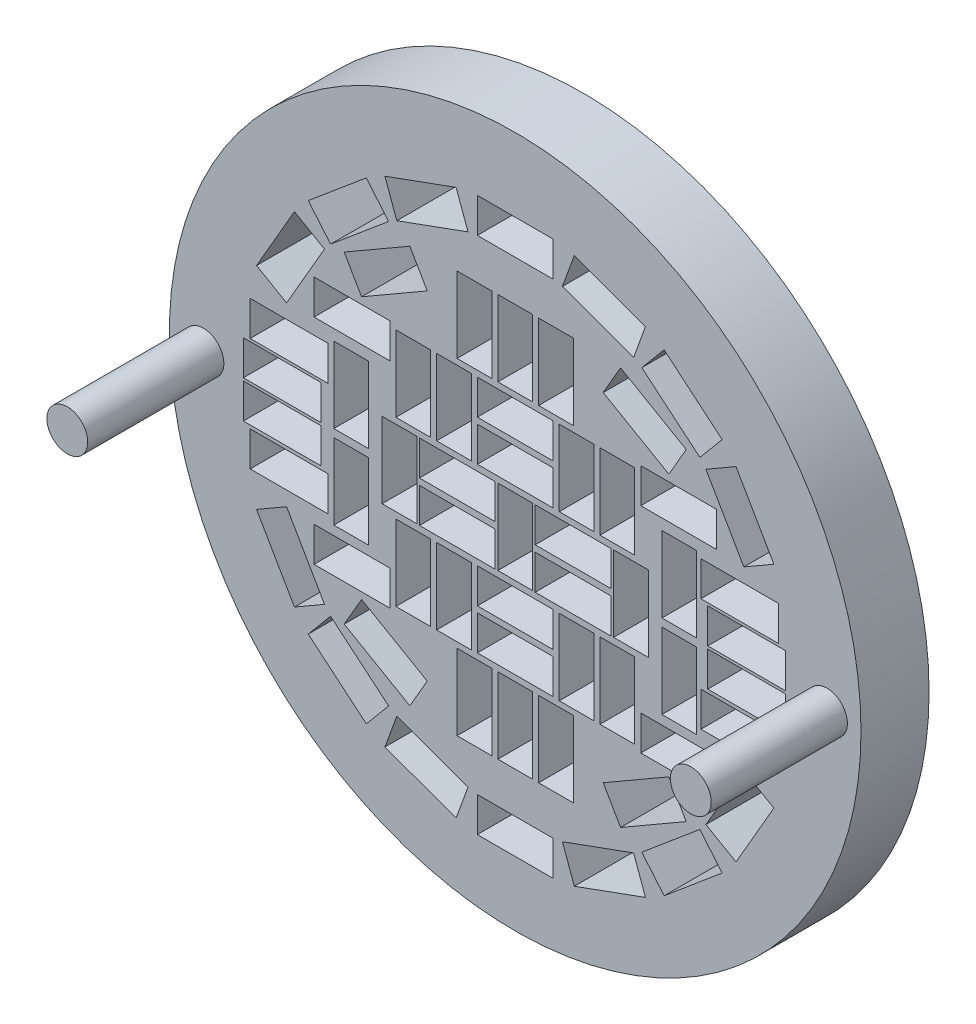
SolidWorks part; units mm, degrees
material "PBT à usage général"
ref_plane "Plan de face" through (0, 0, 0) normal (0, 0, 1) x (1, 0, 0)
ref_plane "Plan de dessus" through (0, 0, 0) normal (0, 1, 0) x (1, 0, 0)
ref_plane "Plan de droite" through (0, 0, 0) normal (1, 0, 0) x (0, 0, -1)
sketch "Esquisse1" plane through (0, 0, 0) normal (0, 0, 1) x (1, 0, 0)
  circle A0 centre (16.6252, 7.1087) radius 25.4
  dimension "D1" = 50.8
extrude "Boss.-Extru.1" add sketch "Esquisse1" along normal blind 5
sketch "Esquisse2" plane through (0, 0, 5) normal (0, 0, 1) x (1, 0, 0)
  line L0 (15.1552, 7.0089) -> (15.1552, 9.5589)
  line L1 (23.8502, 4.0022) -> (23.8502, 9.5672)
  line L2 (15.3502, 4.0022) -> (17.9002, 4.0022)
  line L3 (15.3502, 4.0022) -> (15.3502, 9.5672)
  line L4 (15.3502, 9.5672) -> (17.9002, 9.5672)
  line L5 (17.9002, 4.0022) -> (17.9002, 9.5672)
  line L6 (15.3502, 4.0022) -> (17.9002, 9.5672) construction
  line L7 (15.3502, 9.5672) -> (17.9002, 4.0022) construction
  line L8 (23.8502, 4.0022) -> (26.4002, 4.0022)
  line L9 (26.4002, 4.0022) -> (26.4002, 9.5672)
  line L10 (23.8502, 9.5672) -> (26.4002, 9.5672)
  line L11 (23.8502, 16.0022) -> (23.8502, 21.5672) [skipped]
  line L12 (23.8502, 16.0022) -> (26.4002, 16.0022) [skipped]
  line L13 (26.4002, 16.0022) -> (26.4002, 21.5672) [skipped]
  line L14 (23.8502, 21.5672) -> (26.4002, 21.5672) [skipped]
  line L15 (15.3502, 16.0022) -> (15.3502, 21.5672)
  line L16 (15.3502, 16.0022) -> (17.9002, 16.0022)
  line L17 (17.9002, 16.0022) -> (17.9002, 21.5672)
  line L18 (15.3502, 21.5672) -> (17.9002, 21.5672)
  line L19 (6.8502, 4.0022) -> (6.8502, 9.5672)
  line L20 (6.8502, 4.0022) -> (9.4002, 4.0022)
  line L21 (9.4002, 4.0022) -> (9.4002, 9.5672)
  line L22 (6.8502, 9.5672) -> (9.4002, 9.5672)
  line L23 (6.8502, -7.9978) -> (6.8502, -2.4328) [skipped]
  line L24 (6.8502, -7.9978) -> (9.4002, -7.9978) [skipped]
  line L25 (9.4002, -7.9978) -> (9.4002, -2.4328) [skipped]
  line L26 (6.8502, -2.4328) -> (9.4002, -2.4328) [skipped]
  line L27 (15.3502, -7.9978) -> (15.3502, -2.4328)
  line L28 (15.3502, -7.9978) -> (17.9002, -7.9978)
  line L29 (17.9002, -7.9978) -> (17.9002, -2.4328)
  line L30 (15.3502, -2.4328) -> (17.9002, -2.4328)
  line L31 (23.6552, 7.0089) -> (18.0902, 7.0089)
  line L32 (15.3502, 21.5672) -> (17.9002, 16.0022) construction
  line L33 (23.6552, 7.0089) -> (23.6552, 9.5589)
  line L34 (23.6552, 9.5589) -> (18.0902, 9.5589)
  line L35 (18.0902, 7.0089) -> (18.0902, 9.5589)
  line L36 (23.6552, 7.0089) -> (18.0902, 9.5589) construction
  line L37 (23.6552, 9.5589) -> (18.0902, 7.0089) construction
  line L38 (15.1552, 7.0089) -> (9.5902, 7.0089)
  line L39 (9.5902, 7.0089) -> (9.5902, 9.5589)
  line L40 (15.1552, 9.5589) -> (9.5902, 9.5589)
  line L41 (15.1552, 3.9889) -> (15.1552, 6.5389)
  line L42 (15.1552, 3.9889) -> (9.5902, 3.9889)
  line L43 (9.5902, 3.9889) -> (9.5902, 6.5389)
  line L44 (15.1552, 6.5389) -> (9.5902, 6.5389)
  line L45 (23.6552, 3.9889) -> (23.6552, 6.5389)
  line L46 (23.6552, 3.9889) -> (18.0902, 3.9889)
  line L47 (18.0902, 3.9889) -> (18.0902, 6.5389)
  line L48 (23.6552, 6.5389) -> (18.0902, 6.5389)
  line L49 (16.6252, 6.7847) -> (16.6252, 18.7847) construction
  line L50 (19.4077, 1.0032) -> (19.4077, 3.5532)
  line L51 (19.4077, 10.0102) -> (13.8427, 10.0102)
  line L52 (19.4077, 10.0102) -> (19.4077, 12.5602)
  line L53 (19.4077, 12.5602) -> (13.8427, 12.5602)
  line L54 (13.8427, 10.0102) -> (13.8427, 12.5602)
  line L55 (19.4077, 10.0102) -> (13.8427, 12.5602) construction
  line L56 (19.4077, 12.5602) -> (13.8427, 10.0102) construction
  line L57 (19.4077, 13.0032) -> (13.8427, 13.0032)
  line L58 (19.4077, 13.0032) -> (19.4077, 15.5532)
  line L59 (19.4077, 15.5532) -> (13.8427, 15.5532)
  line L60 (13.8427, 13.0032) -> (13.8427, 15.5532)
  line L61 (19.4077, 13.0032) -> (13.8427, 15.5532) construction
  line L62 (19.4077, 15.5532) -> (13.8427, 13.0032) construction
  line L63 (19.4077, 1.0032) -> (13.8427, 1.0032)
  line L64 (13.8427, 1.0032) -> (13.8427, 3.5532)
  line L65 (19.4077, 3.5532) -> (13.8427, 3.5532)
  line L66 (19.4077, -1.9898) -> (19.4077, 0.5602)
  line L67 (19.4077, -1.9898) -> (13.8427, -1.9898)
  line L68 (13.8427, -1.9898) -> (13.8427, 0.5602)
  line L69 (19.4077, 0.5602) -> (13.8427, 0.5602)
  line L70 (16.6252, 12.7847) -> (12.1247, 12.7847) construction
  line L71 (10.8497, 10.0022) -> (13.3997, 10.0022)
  line L72 (10.8497, 10.0022) -> (10.8497, 15.5672)
  line L73 (10.8497, 15.5672) -> (13.3997, 15.5672)
  line L74 (13.3997, 10.0022) -> (13.3997, 15.5672)
  line L75 (10.8497, 10.0022) -> (13.3997, 15.5672) construction
  line L76 (10.8497, 15.5672) -> (13.3997, 10.0022) construction
  line L77 (7.8597, 10.0022) -> (7.8597, 15.5672)
  line L78 (7.8597, 10.0022) -> (10.4097, 10.0022)
  line L79 (10.4097, 10.0022) -> (10.4097, 15.5672)
  line L80 (7.8597, 15.5672) -> (10.4097, 15.5672)
  line L81 (19.8597, 10.0022) -> (19.8597, 15.5672)
  line L82 (19.8597, 15.5672) -> (22.4097, 15.5672)
  line L83 (22.4097, 10.0022) -> (22.4097, 15.5672)
  line L84 (19.8597, 10.0022) -> (22.4097, 10.0022)
  line L85 (22.8497, 10.0022) -> (22.8497, 15.5672)
  line L86 (22.8497, 10.0022) -> (25.3997, 10.0022)
  line L87 (25.3997, 10.0022) -> (25.3997, 15.5672)
  line L88 (22.8497, 15.5672) -> (25.3997, 15.5672)
  line L89 (19.8597, -2.0278) -> (19.8597, 3.5372)
  line L90 (19.8597, 3.5372) -> (22.4097, 3.5372)
  line L91 (22.4097, -2.0278) -> (22.4097, 3.5372)
  line L92 (19.8597, -2.0278) -> (22.4097, -2.0278)
  line L93 (22.8497, -2.0278) -> (22.8497, 3.5372)
  line L94 (22.8497, -2.0278) -> (25.3997, -2.0278)
  line L95 (25.3997, -2.0278) -> (25.3997, 3.5372)
  line L96 (22.8497, 3.5372) -> (25.3997, 3.5372)
  line L97 (7.8597, -2.0278) -> (7.8597, 3.5372)
  line L98 (7.8597, 3.5372) -> (10.4097, 3.5372)
  line L99 (10.4097, -2.0278) -> (10.4097, 3.5372)
  line L100 (7.8597, -2.0278) -> (10.4097, -2.0278)
  line L101 (10.8497, -2.0278) -> (10.8497, 3.5372)
  line L102 (10.8497, -2.0278) -> (13.3997, -2.0278)
  line L103 (13.3997, -2.0278) -> (13.3997, 3.5372)
  line L104 (10.8497, 3.5372) -> (13.3997, 3.5372)
  line L105 (25.3219, 22.5432) -> (26.194, 24.9394)
  line L106 (19.4077, 24.5672) -> (13.8427, 24.5672)
  line L107 (19.4077, 24.5672) -> (19.4077, 27.1172)
  line L108 (19.4077, 27.1172) -> (13.8427, 27.1172)
  line L109 (13.8427, 24.5672) -> (13.8427, 27.1172)
  line L110 (19.4077, 24.5672) -> (13.8427, 27.1172) construction
  line L111 (19.4077, 27.1172) -> (13.8427, 24.5672) construction
  line L112 (25.3219, 22.5432) -> (20.0925, 24.4465)
  line L113 (20.0925, 24.4465) -> (20.9646, 26.8427)
  line L114 (26.194, 24.9394) -> (20.9646, 26.8427)
  line L115 (30.1871, 18.6184) -> (31.8262, 20.5718)
  line L116 (30.1871, 18.6184) -> (25.9241, 22.1955)
  line L117 (25.9241, 22.1955) -> (27.5632, 24.1489)
  line L118 (31.8262, 20.5718) -> (27.5632, 24.1489)
  line L119 (33.4166, 13.2663) -> (35.6249, 14.5413)
  line L120 (33.4166, 13.2663) -> (30.6341, 18.0857)
  line L121 (30.6341, 18.0857) -> (32.8424, 19.3607)
  line L122 (35.6249, 14.5413) -> (32.8424, 19.3607)
  line L123 (34.6207, 7.1324) -> (37.132, 7.5752) [skipped]
  line L124 (34.6207, 7.1324) -> (33.6544, 12.6129) [skipped]
  line L125 (33.6544, 12.6129) -> (36.1656, 13.0557) [skipped]
  line L126 (37.132, 7.5752) -> (36.1656, 13.0557) [skipped]
  line L127 (33.6544, 0.9566) -> (36.1656, 0.5138) [skipped]
  line L128 (33.6544, 0.9566) -> (34.6207, 6.4371) [skipped]
  line L129 (34.6207, 6.4371) -> (37.132, 5.9943) [skipped]
  line L130 (36.1656, 0.5138) -> (37.132, 5.9943) [skipped]
  line L131 (30.6341, -4.5162) -> (32.8424, -5.7912)
  line L132 (30.6341, -4.5162) -> (33.4166, 0.3032)
  line L133 (33.4166, 0.3032) -> (35.6249, -0.9718)
  line L134 (32.8424, -5.7912) -> (35.6249, -0.9718)
  line L135 (25.9241, -8.626) -> (27.5632, -10.5794)
  line L136 (25.9241, -8.626) -> (30.1871, -5.0489)
  line L137 (30.1871, -5.0489) -> (31.8262, -7.0023)
  line L138 (27.5632, -10.5794) -> (31.8262, -7.0023)
  line L139 (20.0925, -10.877) -> (20.9646, -13.2732)
  line L140 (20.0925, -10.877) -> (25.3219, -8.9737)
  line L141 (25.3219, -8.9737) -> (26.194, -11.3699)
  line L142 (20.9646, -13.2732) -> (26.194, -11.3699)
  line L143 (13.8427, -10.9978) -> (13.8427, -13.5478)
  line L144 (13.8427, -10.9978) -> (19.4077, -10.9978)
  line L145 (19.4077, -10.9978) -> (19.4077, -13.5478)
  line L146 (13.8427, -13.5478) -> (19.4077, -13.5478)
  line L147 (7.9285, -8.9737) -> (7.0564, -11.3699)
  line L148 (7.9285, -8.9737) -> (13.1579, -10.877)
  line L149 (13.1579, -10.877) -> (12.2858, -13.2732)
  line L150 (7.0564, -11.3699) -> (12.2858, -13.2732)
  line L151 (3.0633, -5.0489) -> (1.4242, -7.0023)
  line L152 (3.0633, -5.0489) -> (7.3264, -8.626)
  line L153 (7.3264, -8.626) -> (5.6872, -10.5794)
  line L154 (1.4242, -7.0023) -> (5.6872, -10.5794)
  line L155 (-0.1661, 0.3032) -> (-2.3745, -0.9718)
  line L156 (-0.1661, 0.3032) -> (2.6164, -4.5162)
  line L157 (2.6164, -4.5162) -> (0.408, -5.7912)
  line L158 (-2.3745, -0.9718) -> (0.408, -5.7912)
  line L159 (-1.3703, 6.4371) -> (-3.8816, 5.9943) [skipped]
  line L160 (-1.3703, 6.4371) -> (-0.404, 0.9566) [skipped]
  line L161 (-0.404, 0.9566) -> (-2.9152, 0.5138) [skipped]
  line L162 (-3.8816, 5.9943) -> (-2.9152, 0.5138) [skipped]
  line L163 (-0.404, 12.6129) -> (-2.9152, 13.0557) [skipped]
  line L164 (-0.404, 12.6129) -> (-1.3703, 7.1324) [skipped]
  line L165 (-1.3703, 7.1324) -> (-3.8816, 7.5752) [skipped]
  line L166 (-2.9152, 13.0557) -> (-3.8816, 7.5752) [skipped]
  line L167 (2.6164, 18.0857) -> (0.408, 19.3607)
  line L168 (2.6164, 18.0857) -> (-0.1661, 13.2663)
  line L169 (-0.1661, 13.2663) -> (-2.3745, 14.5413)
  line L170 (0.408, 19.3607) -> (-2.3745, 14.5413)
  line L171 (7.3264, 22.1955) -> (5.6872, 24.1489)
  line L172 (7.3264, 22.1955) -> (3.0633, 18.6184)
  line L173 (3.0633, 18.6184) -> (1.4242, 20.5718)
  line L174 (5.6872, 24.1489) -> (1.4242, 20.5718)
  line L179 (14.9032, 21.5612) -> (14.9032, 15.9962)
  line L180 (20.8932, 21.5612) -> (18.3432, 21.5612)
  line L181 (20.8932, 21.5612) -> (20.8932, 15.9962)
  line L182 (20.8932, 15.9962) -> (18.3432, 15.9962)
  line L183 (18.3432, 21.5612) -> (18.3432, 15.9962)
  line L184 (20.8932, 21.5612) -> (18.3432, 15.9962) construction
  line L185 (20.8932, 15.9962) -> (18.3432, 21.5612) construction
  line L186 (14.9032, 21.5612) -> (12.3532, 21.5612)
  line L187 (12.3532, 21.5612) -> (12.3532, 15.9962)
  line L188 (14.9032, 15.9962) -> (12.3532, 15.9962)
  line L189 (14.9032, -2.4388) -> (14.9032, -8.0038)
  line L190 (14.9032, -2.4388) -> (12.3532, -2.4388)
  line L191 (12.3532, -2.4388) -> (12.3532, -8.0038)
  line L192 (14.9032, -8.0038) -> (12.3532, -8.0038)
  line L193 (20.8932, -2.4388) -> (20.8932, -8.0038)
  line L194 (20.8932, -2.4388) -> (18.3432, -2.4388)
  line L195 (18.3432, -2.4388) -> (18.3432, -8.0038)
  line L196 (20.8932, -8.0038) -> (18.3432, -8.0038)
  line L197 (5.8502, 7.0089) -> (5.8502, 12.5739)
  line L198 (29.9502, 7.0089) -> (27.4002, 7.0089)
  line L199 (29.9502, 7.0089) -> (29.9502, 12.5739)
  line L200 (29.9502, 12.5739) -> (27.4002, 12.5739)
  line L201 (27.4002, 7.0089) -> (27.4002, 12.5739)
  line L202 (29.9502, 7.0089) -> (27.4002, 12.5739) construction
  line L203 (29.9502, 12.5739) -> (27.4002, 7.0089) construction
  line L204 (5.8502, 7.0089) -> (3.3002, 7.0089)
  line L205 (3.3002, 7.0089) -> (3.3002, 12.5739)
  line L206 (5.8502, 12.5739) -> (3.3002, 12.5739)
  line L207 (5.8502, 0.8689) -> (5.8502, 6.4339)
  line L208 (5.8502, 0.8689) -> (3.3002, 0.8689)
  line L209 (3.3002, 0.8689) -> (3.3002, 6.4339)
  line L210 (5.8502, 6.4339) -> (3.3002, 6.4339)
  line L211 (29.9502, 0.8689) -> (29.9502, 6.4339)
  line L212 (29.9502, 0.8689) -> (27.4002, 0.8689)
  line L213 (27.4002, 0.8689) -> (27.4002, 6.4339)
  line L214 (29.9502, 6.4339) -> (27.4002, 6.4339)
  line L219 (13.1579, 24.4465) -> (12.2858, 26.8427)
  line L220 (13.1579, 24.4465) -> (7.9285, 22.5432)
  line L221 (7.9285, 22.5432) -> (7.0564, 24.9394)
  line L222 (12.2858, 26.8427) -> (7.0564, 24.9394)
  point P0 (16.6252, 18.7847)
  point P1 (16.6252, 18.7847)
  point P2 (20.8727, 8.2839)
  point P5 (16.6252, 6.7847)
  point P50 (16.6252, 11.2852)
  point P55 (16.6252, 14.2782)
  point P60 (12.1247, 12.7847)
  point P75 (16.6252, 25.8422)
  point P76 (9.1347, 12.7847)
  point P109 (19.6182, 18.7787)
  point P180 (16.6252, 6.7847)
  point P183 (28.6752, 9.7914)
  dimension "D1" = 5.565
  dimension "D2" = 2.55
  dimension "D7" = 12
  dimension "D8" = 0.19
  dimension "D11" = 0.443
  dimension "D12" = 0.443
  dimension "D14" = 2
  dimension "D15" = 0.443
  dimension "D18" = 3
  dimension "D20" = 0.443
  dimension "D21" = 0.443
  dimension "D24" = 1
  dimension "D3" = 2
  dimension "D4" = 2
  dimension "D5" = 2
  dimension "D6" = 2
  dimension "D9" = 2
  dimension "D10" = 2
  dimension "D13" = 2
  dimension "D16" = 2
  dimension "D17" = 2
  dimension "D22" = 2
  dimension "D23" = 2
  dimension "D25" = 2
  dimension "D26" = 2
  dimension "D19" = 18
extrude "Enlèv. mat.-Extru.1" cut sketch "Esquisse2" against normal through all
sketch "Esquisse3" plane through (0, 0, 5) normal (0, 0, 1) x (1, 0, 0)
  line L0 (3.3002, 12.5739) -> (3.3002, 7.0089) construction
  line L1 (2.8572, 9.6672) -> (-2.8428, 9.6672)
  line L2 (2.8572, 9.6672) -> (2.8572, 12.2172)
  line L3 (2.8572, 12.2172) -> (-2.8428, 12.2172)
  line L4 (-2.8428, 9.6672) -> (-2.8428, 12.2172)
  line L5 (2.8572, 9.6672) -> (-2.8428, 12.2172) construction
  line L6 (2.8572, 12.2172) -> (-2.8428, 9.6672) construction
  line L7 (9.4002, 9.5672) -> (6.8502, 9.5672) construction
  line L8 (35.9672, 9.6672) -> (35.9672, 12.2172)
  line L9 (35.9672, 9.6672) -> (30.2672, 9.6672)
  line L10 (30.2672, 9.6672) -> (30.2672, 12.2172)
  line L11 (35.9672, 12.2172) -> (30.2672, 12.2172)
  line L12 (35.9672, 1.3672) -> (35.9672, 3.9172)
  line L13 (35.9672, 1.3672) -> (30.2672, 1.3672)
  line L14 (30.2672, 1.3672) -> (30.2672, 3.9172)
  line L15 (35.9672, 3.9172) -> (30.2672, 3.9172)
  line L16 (2.8572, 1.3672) -> (2.8572, 3.9172)
  line L17 (2.8572, 1.3672) -> (-2.8428, 1.3672)
  line L18 (-2.8428, 1.3672) -> (-2.8428, 3.9172)
  line L19 (2.8572, 3.9172) -> (-2.8428, 3.9172)
  line L20 (36.4672, 6.9172) -> (36.4672, 9.4672)
  line L21 (2.3572, 6.9172) -> (-3.3428, 6.9172)
  line L22 (2.3572, 6.9172) -> (2.3572, 9.4672)
  line L23 (2.3572, 9.4672) -> (-3.3428, 9.4672)
  line L24 (-3.3428, 6.9172) -> (-3.3428, 9.4672)
  line L25 (2.3572, 6.9172) -> (-3.3428, 9.4672) construction
  line L26 (2.3572, 9.4672) -> (-3.3428, 6.9172) construction
  line L27 (36.4672, 6.9172) -> (30.7672, 6.9172)
  line L28 (30.7672, 6.9172) -> (30.7672, 9.4672)
  line L29 (36.4672, 9.4672) -> (30.7672, 9.4672)
  line L30 (36.4672, 4.1672) -> (36.4672, 6.7172)
  line L31 (36.4672, 4.1672) -> (30.7672, 4.1672)
  line L32 (30.7672, 4.1672) -> (30.7672, 6.7172)
  line L33 (36.4672, 6.7172) -> (30.7672, 6.7172)
  line L34 (2.3572, 4.1672) -> (2.3572, 6.7172)
  line L35 (2.3572, 4.1672) -> (-3.3428, 4.1672)
  line L36 (-3.3428, 4.1672) -> (-3.3428, 6.7172)
  line L37 (2.3572, 6.7172) -> (-3.3428, 6.7172)
  point P0 (0.0072, 10.9422)
  point P9 (-0.4928, 8.1922)
  point P26 (2.3572, 8.1922)
  dimension "D1" = 5.7
  dimension "D2" = 2.55
  dimension "D3" = 0.443
  dimension "D4" = 0.1
  dimension "D7" = 0.2
  dimension "D8" = 0.5
  dimension "D5" = 2
  dimension "D6" = 2
  dimension "D9" = 2
  dimension "D10" = 2
extrude "Enlèv. mat.-Extru.2" cut sketch "Esquisse3" against normal through all
sketch "Esquisse4" plane through (0, 0, 5) normal (0, 0, 1) x (1, 0, 0)
  line L0 (25.8467, 13.3739) -> (25.8467, 15.9239)
  line L1 (1.8467, 13.3739) -> (7.4167, 13.3739)
  line L2 (1.8467, 13.3739) -> (1.8467, 15.9239)
  line L3 (1.8467, 15.9239) -> (7.4167, 15.9239)
  line L4 (7.4167, 13.3739) -> (7.4167, 15.9239)
  line L5 (1.8467, 13.3739) -> (7.4167, 15.9239) construction
  line L6 (1.8467, 15.9239) -> (7.4167, 13.3739) construction
  line L7 (7.8597, 15.5672) -> (7.8597, 10.0022) construction
  line L8 (5.8502, 12.5739) -> (3.3002, 12.5739) construction
  line L9 (25.8467, 13.3739) -> (31.4167, 13.3739)
  line L10 (31.4167, 13.3739) -> (31.4167, 15.9239)
  line L11 (25.8467, 15.9239) -> (31.4167, 15.9239)
  line L12 (25.8467, -2.3561) -> (25.8467, 0.1939)
  line L13 (25.8467, -2.3561) -> (31.4167, -2.3561)
  line L14 (31.4167, -2.3561) -> (31.4167, 0.1939)
  line L15 (25.8467, 0.1939) -> (31.4167, 0.1939)
  line L16 (1.8467, -2.3561) -> (1.8467, 0.1939)
  line L17 (1.8467, -2.3561) -> (7.4167, -2.3561)
  line L18 (7.4167, -2.3561) -> (7.4167, 0.1939)
  line L19 (1.8467, 0.1939) -> (7.4167, 0.1939)
  line L28 (-8.7748, 7.1087) -> (16.6252, 7.1087) construction
  line L29 (3.0633, 18.6184) -> (5.2533, 18.6184) construction
  line L30 (4.0633, 18.6184) -> (8.8871, 21.4034)
  line L31 (8.8871, 21.4034) -> (28.776, 21.4034) construction
  line L32 (8.8871, 21.4034) -> (10.1621, 19.195)
  line L33 (10.1621, 19.195) -> (5.3383, 16.41)
  line L34 (5.3383, 16.41) -> (4.0633, 18.6184)
  line L35 (10.1621, 19.195) -> (30.3285, 19.195) construction
  line L36 (5.3383, 16.41) -> (30.3285, 16.41) construction
  line L37 (4.0633, 18.6184) -> (31.15, 18.6184) construction
  line L38 (29.1871, 18.6184) -> (24.3633, 21.4034)
  line L39 (29.1871, 18.6184) -> (27.9121, 16.41)
  line L40 (27.9121, 16.41) -> (23.0883, 19.195)
  line L41 (23.0883, 19.195) -> (24.3633, 21.4034)
  line L42 (5.3383, 16.41) -> (5.3383, -8.2495) construction
  line L43 (4.0633, 18.6184) -> (4.0633, -5.0489) construction
  line L44 (10.1621, 19.195) -> (10.1621, -10.5655) construction
  line L45 (8.8871, 21.4034) -> (8.8871, -10.5655) construction
  line L46 (4.0633, -5.0489) -> (8.8871, -7.8339)
  line L47 (4.0633, -5.0489) -> (5.3383, -2.8405)
  line L48 (5.3383, -2.8405) -> (10.1621, -5.6255)
  line L49 (10.1621, -5.6255) -> (8.8871, -7.8339)
  line L50 (4.0633, -5.0489) -> (29.1871, -5.0489) construction
  line L51 (10.1621, -5.6255) -> (28.776, -5.6255) construction
  line L52 (5.3383, -2.8405) -> (30.9686, -2.8405) construction
  line L53 (8.8871, -7.8339) -> (28.297, -7.8339) construction
  line L54 (29.1871, -5.0489) -> (24.3633, -7.8339)
  line L55 (29.1871, -5.0489) -> (27.9121, -2.8405)
  line L56 (27.9121, -2.8405) -> (23.0883, -5.6255)
  line L57 (23.0883, -5.6255) -> (24.3633, -7.8339)
  circle A0 centre (16.6252, 7.1087) radius 25.4 construction
  point P0 (4.6317, 14.6489)
  dimension "D1" = 5.57
  dimension "D2" = 2.55
  dimension "D3" = 0.443
  dimension "D4" = 0.8
  dimension "D7" = 5.57
  dimension "D8" = 2.55
  dimension "D9" = 1
  dimension "D10" = 1
  dimension "D11" = 5.57
  dimension "D12" = 0
  dimension "D13" = 1
  dimension "D14" = 2.55
  dimension "D5" = 2
  dimension "D6" = 2
extrude "Enlèv. mat.-Extru.3" cut sketch "Esquisse4" against normal through all
sketch "Esquisse5" plane through (0, 0, 5) normal (0, 0, 1) x (1, 0, 0)
  line L0 (-8.7748, 7.1087) -> (42.0252, 7.1087) construction
  circle A0 centre (16.6252, 7.1087) radius 25.4 construction
  circle A1 centre (-6.2748, 7.1087) radius 1.5
  circle A2 centre (39.5252, 7.1087) radius 1.5
  point P12 (16.6252, 7.1087)
  dimension "D1" = 3
  dimension "D3" = 2
  dimension "D2" = 2.5
extrude "Boss.-Extru.2" add sketch "Esquisse5" along normal blind 10
